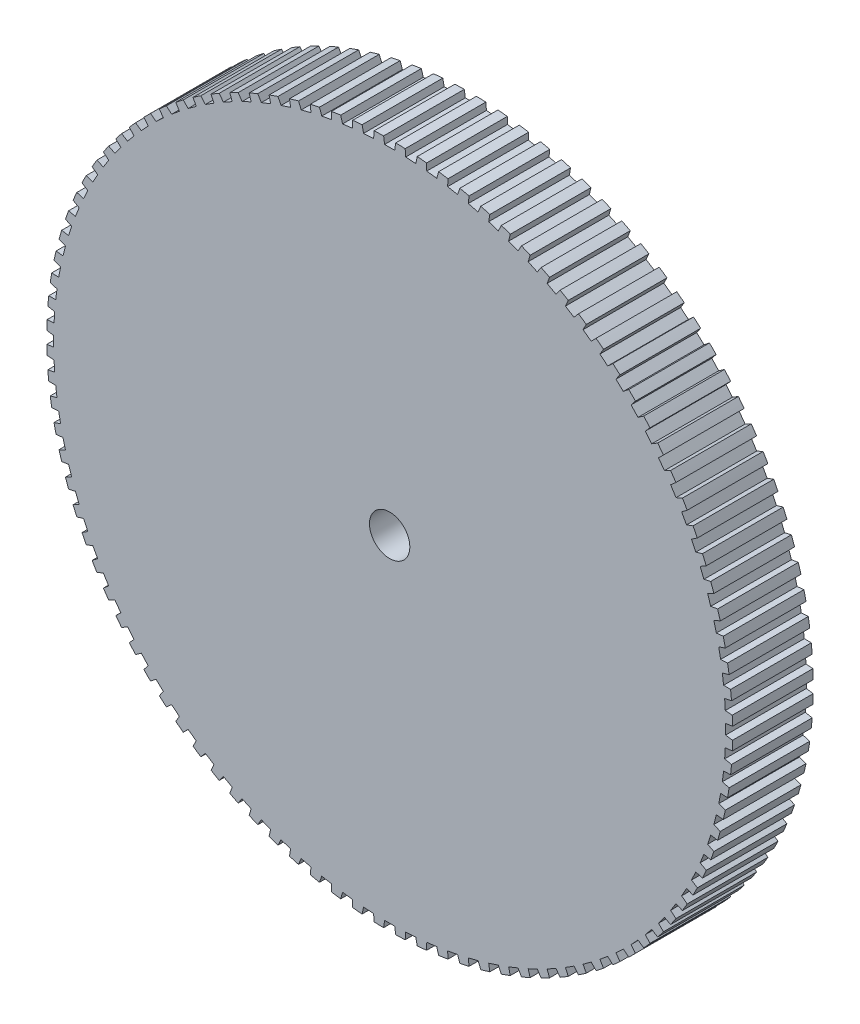
SolidWorks part; units mm, degrees
ref_plane "Front Plane" through (0, 0, 0) normal (0, 0, 1) x (1, 0, 0)
ref_plane "Top Plane" through (0, 0, 0) normal (0, 1, 0) x (1, 0, 0)
ref_plane "Right Plane" through (0, 0, 0) normal (1, 0, 0) x (0, 0, -1)
sketch "Sketch1" plane through (0, 0, 0) normal (0, 0, 1) x (1, 0, 0)
  circle A0 centre (0, 0) radius 37 construction
  circle A2 centre (0, 0) radius 34
  dimension "D1" = 74
  dimension "rubberthk" = 3
extrude "Boss-Extrude1" add sketch "Sketch1" along normal blind 8
sketch "Sketch4" plane through (0, 0, 0) normal (0, 0, -1) x (-1, 0, 0)
  circle A0 centre (0, 0) radius 4.85
  dimension "D1" = 9.7
extrude "Boss-Extrude2" add sketch "Sketch4" along normal blind 8
sketch "Sketch2" plane through (0, 0, 8) normal (0, 0, 1) x (1, 0, 0)
  circle A0 centre (0, 0) radius 4
  dimension "D1" = 8
extrude "Cut-Extrude1" cut sketch "Sketch2" against normal blind 4.35
sketch "Sketch5" plane through (0, 0, 3.65) normal (0, 0, 1) x (1, 0, 0)
  circle A0 centre (0, 0) radius 2
  dimension "D1" = 4
extrude "Cut-Extrude2" cut sketch "Sketch5" against normal offset from surface (4.15 mm away) 7.5 up to face at (-4.85, 0, -8)
sketch "Sketch6" plane through (0, 0, -8) normal (0, 0, -1) x (-1, 0, 0)
  line L0 (2.0785, 1.95) -> (-2.0785, 1.95)
  line L1 (-2.0785, -1.95) -> (2.0785, -1.95)
  arc A0 (2.0785, -1.95) -> (2.0785, 1.95) centre (0, 0) ccw
  arc A1 (-2.0785, 1.95) -> (-2.0785, -1.95) centre (0, 0) ccw
  dimension "D2" = 5.7
  dimension "D1" = 3.9
extrude "Cut-Extrude3" cut sketch "Sketch6" against normal up to surface (7.5 mm away) up to face at (-2, 0, -0.5)
sketch "Sketch7" plane through (0, 0, 8) normal (0, 0, 1) x (1, 0, 0)
  line L0 (-0.6, 33.9947) -> (-0.5, 33.31)
  line L1 (-0.5, 33.31) -> (0.5, 33.31)
  line L2 (0.5, 33.31) -> (0.6, 33.9947)
  line L3 (0, 0) -> (-0.6, 33.9947) construction
  line L4 (0, 0) -> (0.6, 33.9947) construction
  circle A0 centre (0, 0) radius 34 construction
  arc A1 (0.6, 33.9947) -> (-0.6, 33.9947) centre (0, 0) ccw
  point P8 (0, 33.31)
  dimension "D1" = 1
  dimension "D2" = 1.2
  dimension "D3" = 0.69
extrude "Cut-Extrude4" cut sketch "Sketch7" against normal through all
pattern_circular "CirPattern1" count 100 over 360 about axis through (0, 0, 0) along (0, 0, 1) of "Cut-Extrude4"
sketch "Sketch8" plane through (0, 0, 3.65) normal (0, 0, 1) x (1, 0, 0)
  circle A0 centre (0, 0) radius 2 construction
  circle A1 centre (0, 0) radius 4
  circle A2 centre (0, 0) radius 4
  circle A3 centre (0, 0) radius 2
  dimension "D1" = 0
extrude "ReverseCountersink" add sketch "Sketch8" along normal up to surface (4.35 mm away) up to face at (0, 0, 8)
equation "\"width\"= 24"
equation "\"thk\"= 3"
equation "\"holesize\"= 4.2"
equation "\"holedistance\"= ( 20 + 12 ) / 2"
equation "\"threaded_hole\"= 3.9"
equation "\"fillet_radius\"= 2"
equation "\"ground_clearance\"= 25"
equation "\"tire_thk\"= 3"
equation "\"innerwheel_diam\" = \"wheel_diam\"-2*\"tire_thk\""
equation "\"innerwheel_thk\"= 8"
equation "\"wheel_diam\"= 2*(\"width\"/2+\"ground_clearance\")"
equation "\"D1@Sketch1\"=\"wheel_diam\""
equation "\"rubberthk@Sketch1\"=\"tire_thk\""
equation "\"D1@Boss-Extrude1\"=\"innerwheel_thk\""
equation "\"coloursensor_holesize\"= 2.65"
equation "\"hole_to_edge\" = 4"
